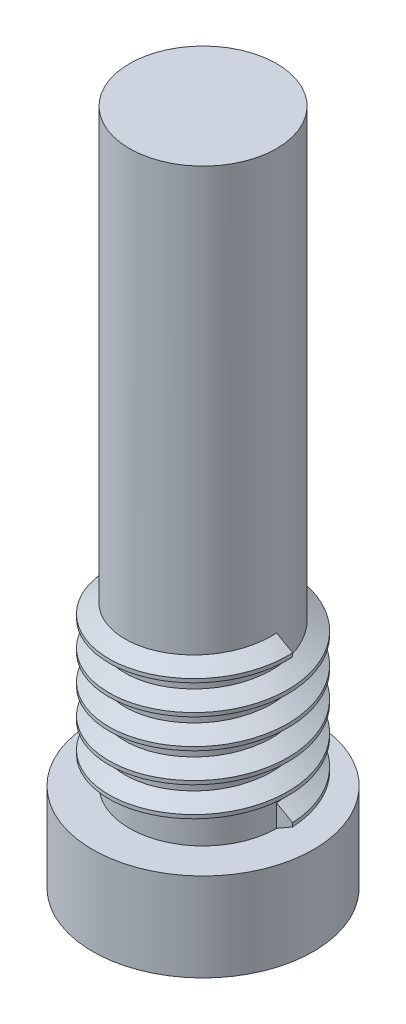
SolidWorks part; units mm, degrees
ref_plane "Front Plane" through (0, 0, 0) normal (0, 0, 1) x (1, 0, 0)
ref_plane "Top Plane" through (0, 0, 0) normal (0, 1, 0) x (1, 0, 0)
ref_plane "Right Plane" through (0, 0, 0) normal (1, 0, 0) x (0, 0, -1)
sketch "Sketch2" plane through (0, 0, 0) normal (0, 1, 0) x (1, 0, 0)
  circle A0 centre (0, 0) radius 4.7625
  dimension "D1" = 9.525
extrude "Boss-Extrude1" add sketch "Sketch2" along normal blind 3.81
sketch "Sketch3" plane through (0, 3.81, 0) normal (0, 1, 0) x (1, 0, 0)
  circle A0 centre (0, 0) radius 3.175
  dimension "D1" = 6.35
extrude "Boss-Extrude2" add sketch "Sketch3" along normal blind 25.4
thread "Thread2" pitch 1.27 profile "Thread Profile2" start angle 0, offset 0, length 6.35, pitch 1.27, diameter 6.35
ref_plane "Plane2" through (3.175, 3.81, 0) normal (0, 0, 1) x (1, 0, 0)
sketch "Thread Profile2" plane through (3.175, 3.81, 0) normal (0, 0, 1) x (1, 0, 0)
  line L0 (0, 0) -> (0, 1.27) construction
  line L1 (0, 0) -> (0.6874, 0.3969)
  line L2 (0.6874, 0.3969) -> (0.6874, 0.5556)
  line L3 (0.6874, 0.5556) -> (0, 0.9525)
  line L4 (0.6874, 0.4762) -> (0, 0.4762) construction
  line L11 (0, 0) -> (0, 0.9525)
  point P2 (0, 0)
  dimension "Pitch" = 1.27
  dimension "Profile_Angle" = 60
  dimension "Profile_Land" = 0.1588
  dimension "Profile_Height" = 0.6874
